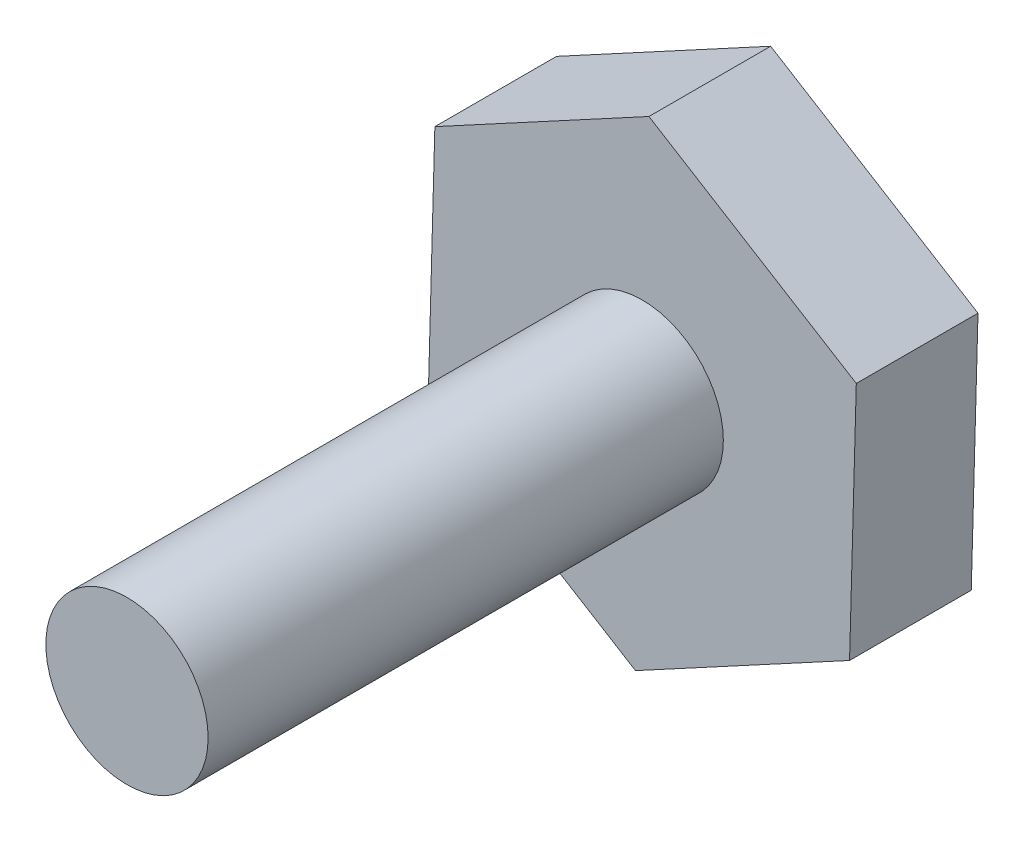
SolidWorks part; units mm, degrees
ref_plane "Front Plane" through (0, 0, 0) normal (0, 0, 1) x (1, 0, 0)
ref_plane "Top Plane" through (0, 0, 0) normal (0, 1, 0) x (1, 0, 0)
ref_plane "Right Plane" through (0, 0, 0) normal (1, 0, 0) x (0, 0, -1)
sketch "Sketch1" plane through (0, 0, 0) normal (0, 0, 1) x (1, 0, 0)
  line L1 (5.2773, 2.8549) -> (0.1662, 5.9977)
  line L2 (0.1662, 5.9977) -> (-5.1111, 3.1428)
  line L3 (-5.1111, 3.1428) -> (-5.2773, -2.8549)
  line L4 (-5.2773, -2.8549) -> (-0.1662, -5.9977)
  line L5 (-0.1662, -5.9977) -> (5.1111, -3.1428)
  line L6 (5.1111, -3.1428) -> (5.2773, 2.8549)
  circle A0 centre (0, 0) radius 5.1962 construction
  dimension "D1" = 6
extrude "Boss-Extrude1" add sketch "Sketch1" along normal blind 3
sketch "Sketch2" plane through (0, 0, 3) normal (0, 0, 1) x (1, 0, 0)
  circle A0 centre (0, 0) radius 2
  dimension "D1" = 4
extrude "Boss-Extrude2" add sketch "Sketch2" along normal blind 12.7
